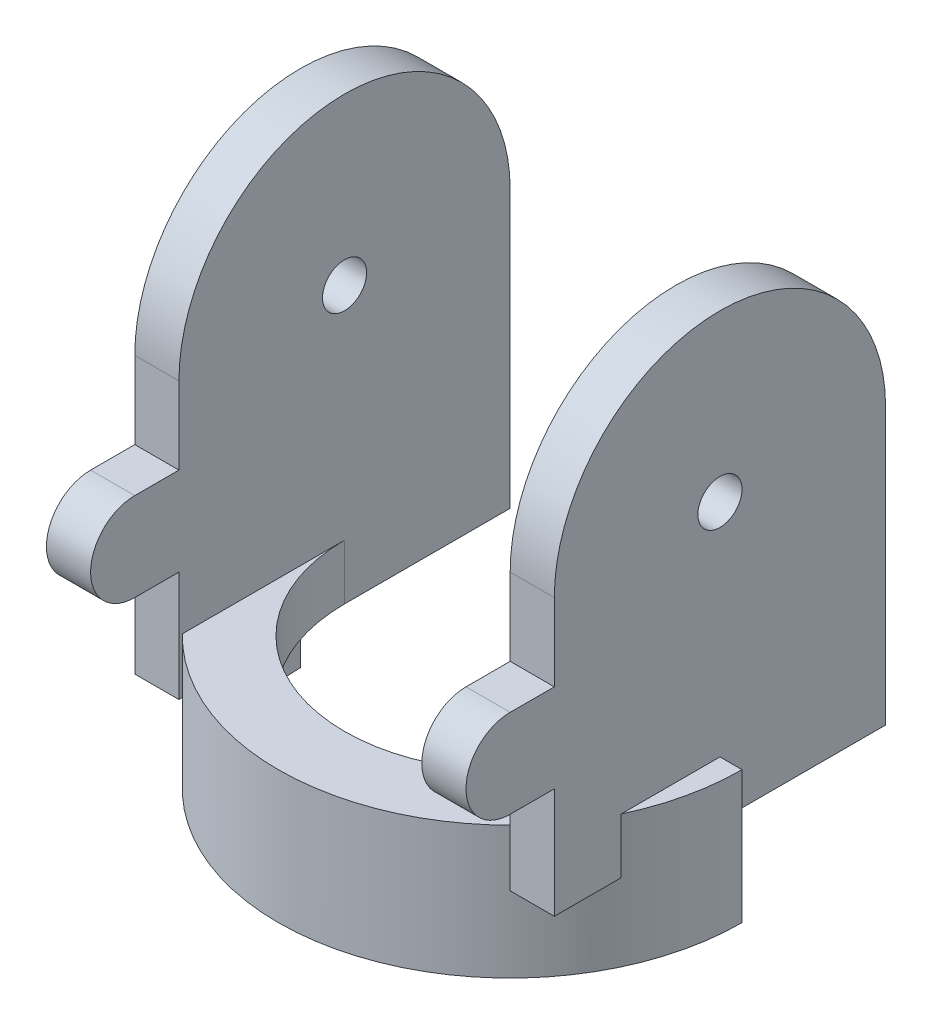
SolidWorks part; units mm, degrees
ref_plane "Front" through (0, 0, 0) normal (0, 0, 1) x (1, 0, 0)
ref_plane "Top" through (0, 0, 0) normal (0, 1, 0) x (1, 0, 0)
ref_plane "Right" through (0, 0, 0) normal (1, 0, 0) x (0, 0, -1)
sketch "草图1" plane through (0, 0, 0) normal (0, 1, 0) x (1, 0, 0)
  circle A0 centre (0, 0) radius 38
  circle A1 centre (0, 0) radius 30
extrude "凸台-拉伸1" add sketch "草图1" along normal blind 10
sketch "草图2" plane through (0, 0, 0) normal (0, -1, 0) x (1, 0, 0)
  line L0 (-38, 0) -> (0, 0) construction
  line L1 (0, 0) -> (0, 38) construction
  line L3 (-38, 30) -> (-30, 30)
  line L4 (-38, 30) -> (-38, -30)
  line L5 (-38, -30) -> (-30, -30)
  line L6 (-30, 30) -> (-30, -30)
  line L7 (38, 30) -> (30, 30)
  line L8 (38, 30) -> (38, -30)
  line L9 (38, -30) -> (30, -30)
  line L10 (30, 30) -> (30, -30)
  circle A0 centre (0, 0) radius 38 construction
  dimension "D1" = 60
  dimension "D2" = 30
  dimension "D3" = 8
  dimension "D4" = 38
  dimension "D5" = 60
  dimension "D6" = 30
  dimension "D7" = 8
extrude "凸台-拉伸2" add sketch "草图2" against normal blind 80
sketch "草图3" plane through (38, 0, 0) normal (1, 0, 0) x (0, 0, -1)
  line L0 (-30, 50) -> (-30, 88)
  line L1 (-30, 88) -> (30, 88)
  line L2 (30, 88) -> (30, 50)
  arc A0 (30, 50) -> (-30, 50) centre (0, 50) ccw
  circle A1 centre (0, 50) radius 4
  dimension "D1" = 38
extrude "切除-拉伸1" cut sketch "草图3" against normal blind 80
sketch "草图4" plane through (0, 0, 0) normal (0, -1, 0) x (1, 0, 0)
  line L1 (-30, 0) -> (30, 0)
  line L2 (-30, 0) -> (-30, -40.6781)
  line L3 (-30, -40.6781) -> (30, -40.6781)
  line L4 (30, 0) -> (30, -40.6781)
extrude "切除-拉伸2" cut sketch "草图4" against normal through all
sketch "草图5" plane through (0, 10, 0) normal (0, 1, 0) x (1, 0, 0)
  line L0 (0, 0) -> (-55.8176, 0) construction
  line L1 (0, 0) -> (48.0726, 0) construction
  line L2 (42, 0) -> (38, 0)
  line L3 (-42, 0) -> (-38, 0)
  arc A0 (-38, 0) -> (38, 0) centre (0, 0) ccw
  arc A1 (-42, 0) -> (42, 0) centre (0, 0) ccw
extrude "凸台-拉伸3" add sketch "草图5" against normal blind 24
sketch "草图7" plane through (0, 0, 30) normal (0, 0, 1) x (1, 0, 0)
  line L0 (-38, 50) -> (-38, 0) construction
  line L1 (-30, 20) -> (-38, 20)
  line L2 (-30, 20) -> (-30, 36)
  line L3 (-30, 36) -> (-38, 36)
  line L4 (-38, 20) -> (-38, 36)
  line L5 (30, 50) -> (30, 0) construction
  line L6 (38, 20) -> (30, 20)
  line L7 (38, 20) -> (38, 36)
  line L8 (38, 36) -> (30, 36)
  line L9 (30, 20) -> (30, 36)
  line L10 (-38, 0) -> (-30, 0) construction
  line L11 (30, 0) -> (38, 0) construction
  dimension "D1" = 16
  dimension "D2" = 16
  dimension "D3" = 20
  dimension "D4" = 20
extrude "凸台-拉伸5" add sketch "草图7" along normal blind 16
sketch "草图8" plane through (38, 0, 0) normal (1, 0, 0) x (0, 0, -1)
  line L1 (-38, 36) -> (-49.7902, 36)
  line L3 (-38, 20) -> (-49.7902, 20)
  line L4 (-49.7902, 36) -> (-49.7902, 20)
  arc A0 (-38, 36) -> (-38, 20) centre (-38, 28) ccw
extrude "切除-拉伸3" cut sketch "草图8" against normal through all
